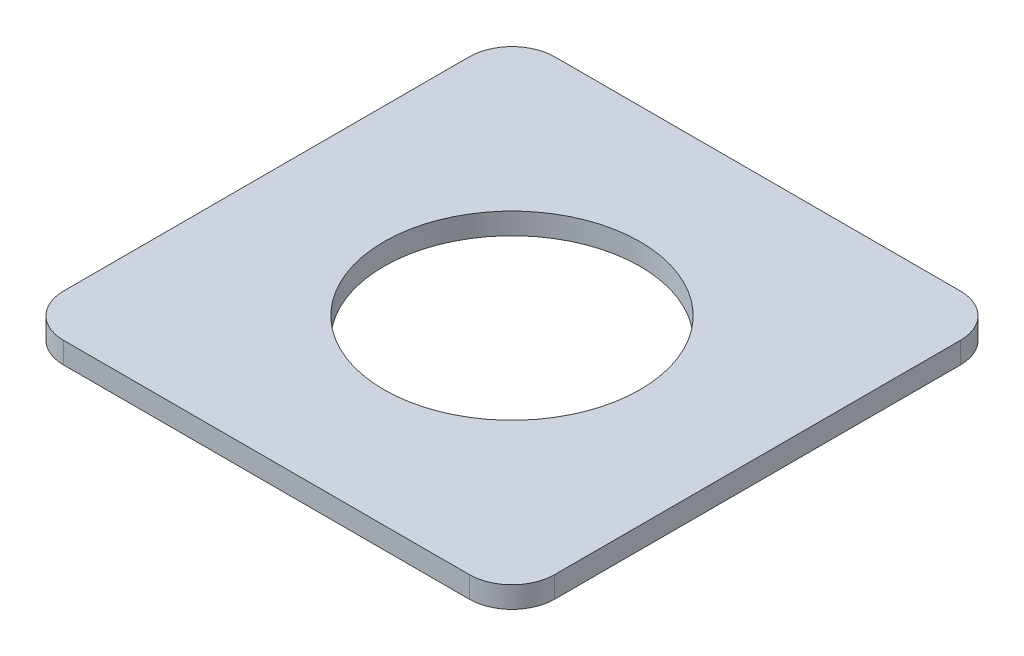
SolidWorks part; units mm, degrees
material "Медь"
ref_plane "Front" through (0, 0, 0) normal (0, 0, 1) x (1, 0, 0)
ref_plane "Top" through (0, 0, 0) normal (0, 1, 0) x (1, 0, 0)
ref_plane "Right" through (0, 0, 0) normal (1, 0, 0) x (0, 0, -1)
sketch "Эскиз2" plane through (0, 0, 0) normal (0, 1, 0) x (1, 0, 0)
  line L1 (9.5, -11.5) -> (-9.5, -11.5)
  line L2 (11.5, -9.5) -> (11.5, 9.5)
  line L3 (9.5, 11.5) -> (-9.5, 11.5)
  line L4 (-11.5, -9.5) -> (-11.5, 9.5)
  line L5 (11.5, -11.5) -> (-11.5, 11.5) construction
  line L6 (11.5, 11.5) -> (-11.5, -11.5) construction
  circle A0 centre (0, 0) radius 6
  arc A1 (-9.5, -11.5) -> (-11.5, -9.5) centre (-9.5, -9.5) cw
  arc A2 (9.5, -11.5) -> (11.5, -9.5) centre (9.5, -9.5) ccw
  arc A3 (9.5, 11.5) -> (11.5, 9.5) centre (9.5, 9.5) cw
  arc A4 (-9.5, 11.5) -> (-11.5, 9.5) centre (-9.5, 9.5) ccw
  point P0 (0, 0)
  dimension "D1" = 12
  dimension "D4" = 2
  dimension "D2" = 23
  dimension "D3" = 23
extrude "Бобышка-Вытянуть1" add sketch "Эскиз2" along normal blind 1
